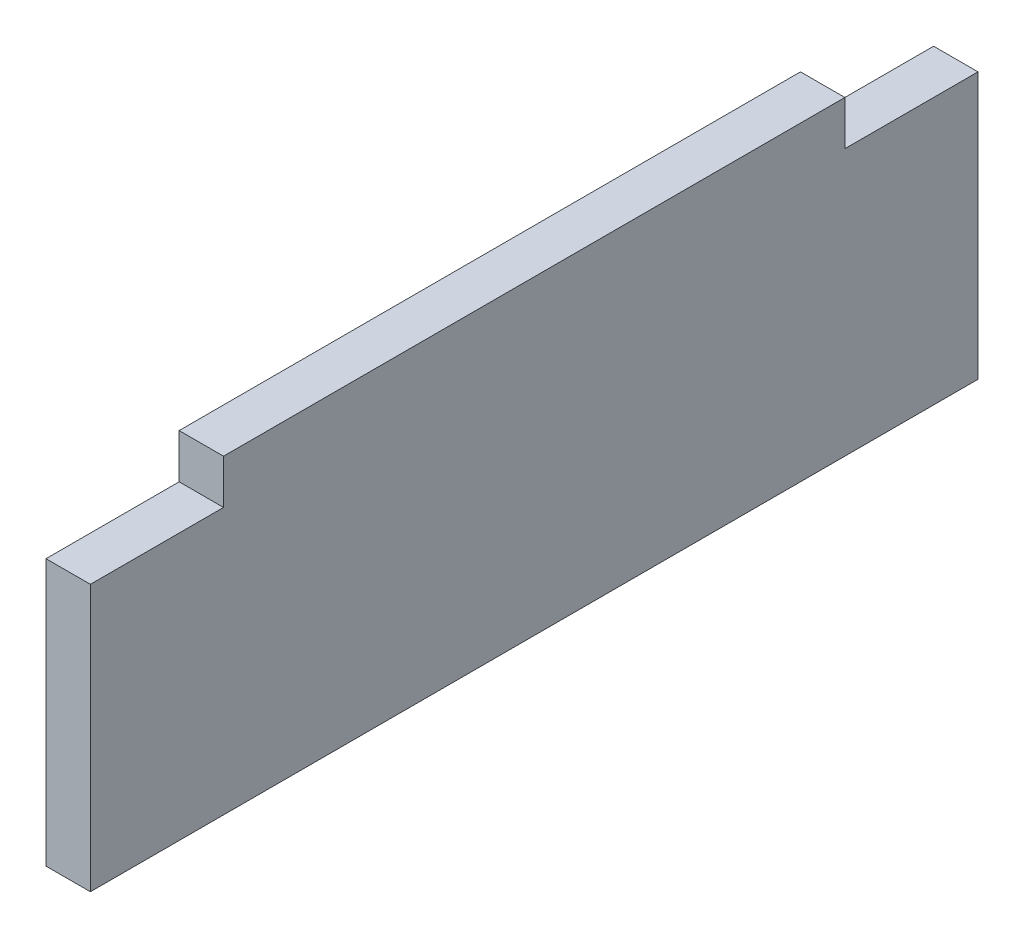
SolidWorks part; units mm, degrees
ref_plane "Front Plane" through (0, 0, 0) normal (0, 0, 1) x (1, 0, 0)
ref_plane "Top Plane" through (0, 0, 0) normal (0, 1, 0) x (1, 0, 0)
ref_plane "Right Plane" through (0, 0, 0) normal (1, 0, 0) x (0, 0, -1)
sketch "Sketch1" plane through (0, 0, 0) normal (1, 0, 0) x (0, 0, -1)
  line L0 (-85, 30) -> (-85, 35)
  line L1 (0, 0) -> (-100, 0)
  line L2 (0, 0) -> (0, 30)
  line L3 (0, 30) -> (-15, 30)
  line L4 (-100, 0) -> (-100, 30)
  line L5 (-85, 35) -> (-15, 35)
  line L6 (-15, 35) -> (-15, 30)
  line L7 (-85, 30) -> (-100, 30)
  dimension "D1" = 30
  dimension "D2" = 70
  dimension "D3" = 100
  dimension "D4" = 15
  dimension "D5" = 5
extrude "Boss-Extrude2" add sketch "Sketch1" along normal blind 5 contours L5 L6 L3 L2 L1 L4 L7 L0
